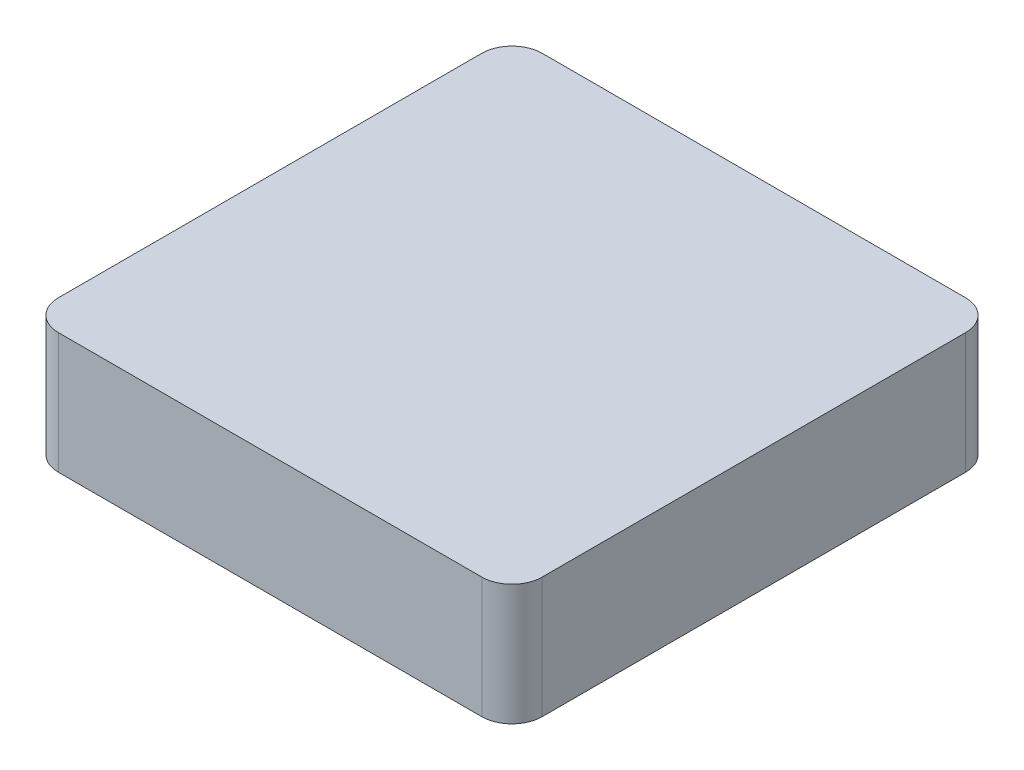
SolidWorks part; units mm, degrees
ref_plane "Face" through (0, 0, 0) normal (0, 0, 1) x (1, 0, 0)
ref_plane "Dessus" through (0, 0, 0) normal (0, 1, 0) x (1, 0, 0)
ref_plane "Droite" through (0, 0, 0) normal (1, 0, 0) x (0, 0, -1)
sketch "Esquisse1" plane through (0, 0, 0) normal (0, 1, 0) x (1, 0, 0)
  line L1 (0, 0) -> (80, 0)
  line L2 (0, 0) -> (0, 80)
  line L3 (0, 80) -> (80, 80)
  line L4 (80, 0) -> (80, 80)
  dimension "D1" = 80
  dimension "D2" = 80
extrude "Extrusion1" add sketch "Esquisse1" along normal blind 20
fillet "Congé1" radius 5 4 edges at (80, 10, -80) (80, 10, 0) (0, 10, 0) (0, 10, -80)
shell "Coque1" thickness 2
